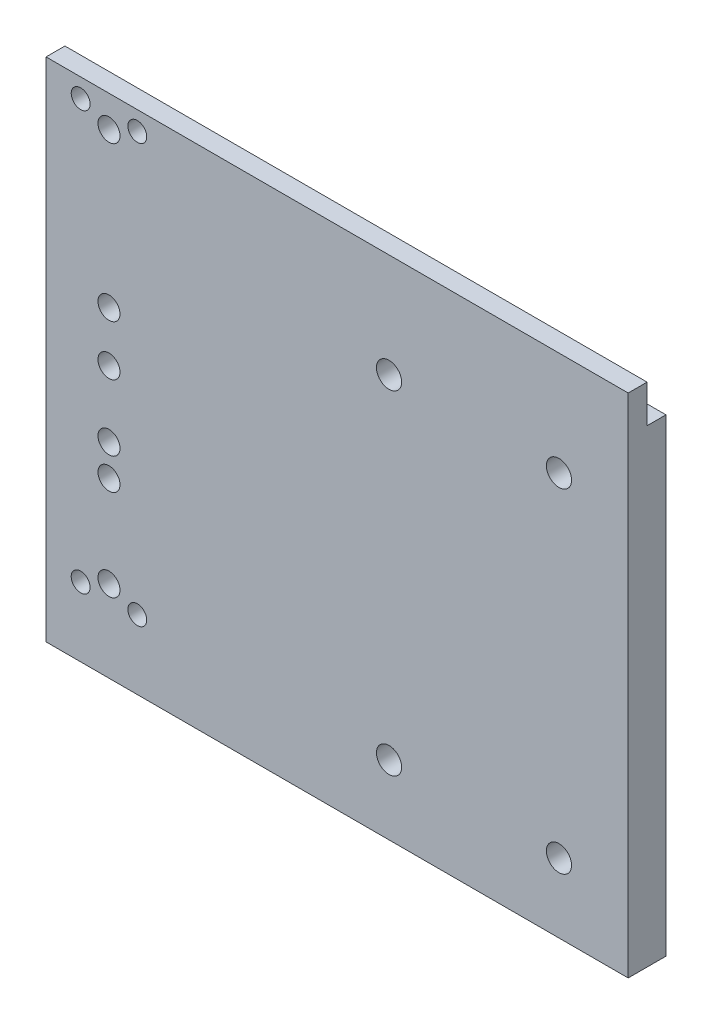
SolidWorks part; units mm, degrees
ref_plane "Front Plane" through (0, 0, 0) normal (0, 0, 1) x (1, 0, 0)
ref_plane "Top Plane" through (0, 0, 0) normal (0, 1, 0) x (1, 0, 0)
ref_plane "Right Plane" through (0, 0, 0) normal (1, 0, 0) x (0, 0, -1)
sketch "Sketch1" plane through (0, 0, 0) normal (0, 0, 1) x (1, 0, 0)
  line L1 (0, 0) -> (97, 0)
  line L2 (0, 0) -> (0, 149)
  line L3 (0, 149) -> (97, 149)
  line L4 (97, 0) -> (97, 149)
  line L5 (21, 128) -> (75, 128) construction
  line L6 (21, 128) -> (21, 22) construction
  line L7 (21, 22) -> (75, 22) construction
  line L8 (75, 128) -> (75, 22) construction
  circle A0 centre (21, 128) radius 4
  circle A1 centre (75, 128) radius 4
  circle A2 centre (75, 22) radius 4
  circle A3 centre (21, 22) radius 4
  dimension "D1" = 98
  dimension "D2" = 46
  dimension "D3" = 8
  dimension "D5" = 18
  dimension "D4" = 18
  dimension "D6" = 17
  dimension "D7" = 17
extrude "Boss-Extrude1" add sketch "Sketch1" against normal blind 6
sketch "Sketch2" plane through (0, 0, 0) normal (0, 0, 1) x (1, 0, 0)
  line L0 (-68, 16) -> (-68, 161) construction
  line L1 (-88, 161) -> (-48, 161)
  line L2 (-88, 161) -> (-88, 16)
  line L3 (-88, 16) -> (-48, 16)
  line L4 (-48, 161) -> (-48, 16)
  line L5 (21, 22) -> (6, 22)
  circle A0 centre (-68, 55) radius 3.5
  circle A1 centre (-68, 65) radius 3.5
  circle A2 centre (-68, 86) radius 3.5
  circle A3 centre (-68, 102) radius 3.5
  circle A4 centre (-77, 22) radius 3
  circle A5 centre (-68, 26) radius 3.5
  circle A6 centre (-59, 22) radius 3
  circle A7 centre (-77, 155) radius 3
  circle A8 centre (-68, 151) radius 3.5
  circle A9 centre (-59, 155) radius 3
  dimension "D1" = 7
  dimension "D2" = 7
  dimension "D3" = 6
  dimension "D4" = 11
  dimension "D5" = 11
  dimension "D6" = 40
  dimension "D7" = 145
  dimension "D8" = 6
  dimension "D9" = 6
  dimension "D10" = 10
  dimension "D11" = 10
  dimension "D12" = 10
  dimension "D13" = 21
  dimension "D14" = 16
  dimension "D15" = 39
  dimension "D16" = 59
  dimension "D17" = 15
  dimension "D18" = 65
sketch "Sketch3" plane through (0, 0, 0) normal (0, 0, 1) x (1, 0, 0)
  line L0 (21, 22) -> (6, 22) construction
  line L1 (-88, 161) -> (97, 161)
  line L2 (-88, 161) -> (-88, 0)
  line L3 (-88, 0) -> (97, 0)
  line L4 (97, 161) -> (97, 0)
  line L5 (21, 22) -> (6, 22)
  circle A1 centre (-77, 155) radius 3
  circle A2 centre (-77, 155) radius 3
  circle A3 centre (-59, 22) radius 3
  circle A4 centre (-59, 22) radius 3
  circle A5 centre (-68, 26) radius 3.5
  circle A6 centre (-68, 26) radius 3.5
  circle A7 centre (-77, 22) radius 3
  circle A8 centre (-77, 22) radius 3
  circle A9 centre (-68, 102) radius 3.5
  circle A10 centre (-68, 102) radius 3.5
  circle A11 centre (-68, 86) radius 3.5
  circle A12 centre (-68, 86) radius 3.5
  circle A13 centre (-68, 65) radius 3.5
  circle A14 centre (-68, 65) radius 3.5
  circle A15 centre (-68, 55) radius 3.5
  circle A16 centre (-68, 55) radius 3.5
  circle A17 centre (-59, 155) radius 3
  circle A18 centre (-59, 155) radius 3
  circle A19 centre (-68, 151) radius 3.5
  circle A20 centre (-68, 151) radius 3.5
  circle A21 centre (21, 22) radius 4
  circle A22 centre (21, 22) radius 4
  circle A23 centre (75, 22) radius 4
  circle A24 centre (75, 22) radius 4
  circle A25 centre (75, 128) radius 4
  circle A26 centre (75, 128) radius 4
  circle A27 centre (21, 128) radius 4
  circle A28 centre (21, 128) radius 4
  dimension "D1" = 0
  dimension "D2" = 0
  dimension "D3" = 0
  dimension "D4" = 0
  dimension "D5" = 0
  dimension "D6" = 0
  dimension "D7" = 0
  dimension "D8" = 0
  dimension "D9" = 0
  dimension "D10" = 0
  dimension "D12" = 0
  dimension "D13" = 0
  dimension "D14" = 0
  dimension "D15" = 0
extrude "Boss-Extrude2" add sketch "Sketch3" along normal blind 6
